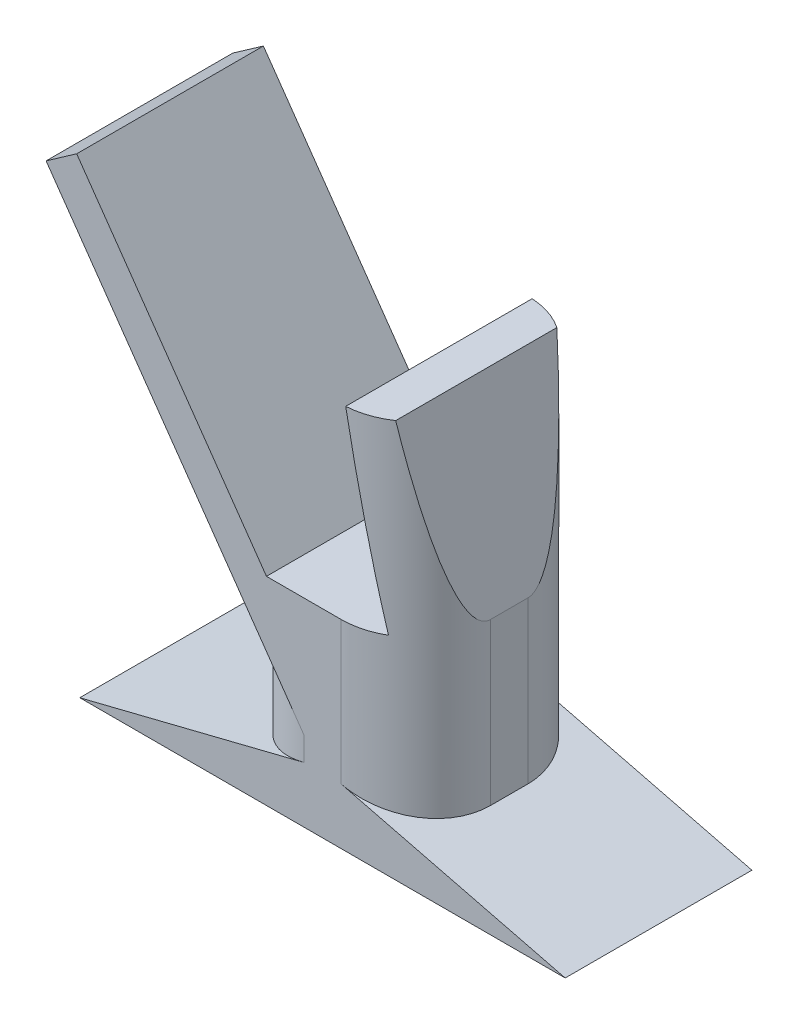
SolidWorks part; units mm, degrees
ref_plane "Front Plane" through (0, 0, 0) normal (0, 0, 1) x (1, 0, 0)
ref_plane "Top Plane" through (0, 0, 0) normal (0, 1, 0) x (1, 0, 0)
ref_plane "Right Plane" through (0, 0, 0) normal (1, 0, 0) x (0, 0, -1)
sketch "Sketch2" plane through (0, 0, 0) normal (0, 0, 1) x (1, 0, 0)
  line L0 (-10.16, 13.5009) -> (-2.54, 13.5009)
  line L1 (0, 0) -> (-12.7, 0)
  line L2 (-12.7, 2.54) -> (-12.7, 12.7)
  line L3 (-12.7, 12.7) -> (-25.1497, 30.48)
  line L4 (0, 13.5009) -> (0, 2.54)
  line L5 (-10.16, 13.5009) -> (-23.069, 31.9369)
  line L6 (-10.16, 2.54) -> (-10.16, 13.5009) construction
  line L7 (0, 2.54) -> (-10.16, 2.54) construction
  line L8 (-23.069, 31.9369) -> (-25.1497, 30.48)
  line L9 (0, 13.5009) -> (-2.2394, 26.2009)
  line L10 (-2.2394, 26.2009) -> (-4.7794, 26.2009)
  line L11 (-4.7794, 26.2009) -> (-2.54, 13.5009)
  line L12 (-12.7, 2.54) -> (-22.86, 0)
  line L13 (-22.86, 0) -> (-12.7, 0)
  line L14 (-6.35, 0) -> (-6.35, 13.5009) construction
  line L15 (10.16, 0) -> (0, 0)
  line L16 (0, 2.54) -> (10.16, 0)
  line L17 (-12.7, 0) -> (-12.7, 12.7) construction
  dimension "D1" = 145
  dimension "D2" = 17.78
  dimension "D3" = 12.7
  dimension "D4" = 12.7
  dimension "D5" = 12.7
  dimension "D6" = 2.54
  dimension "D7" = 80
  dimension "D8" = 10.16
  dimension "D9" = 2.54
extrude "Boss-Extrude1" add sketch "Sketch2" along normal blind 12.7
fillet "Fillet2" radius 5.08 4 edges at (-12.7, 7.62, 12.7) (-12.7, 7.62, 0) (0, 8.0204, 0) (0, 8.0204, 12.7)
sketch "Sketch5" plane through (0, 0, 0) normal (0, -1, 0) x (1, 0, 0)
  line L0 (-6.35, 12.7) -> (-6.35, 0) construction
  line L1 (-22.86, 12.7) -> (10.16, 12.7) construction
  line L2 (-22.86, 0) -> (10.16, 0) construction
  circle A0 centre (-6.35, 6.35) radius 1.27
extrude "Cut-Extrude1" cut sketch "Sketch5" against normal through all both and the other way through all
